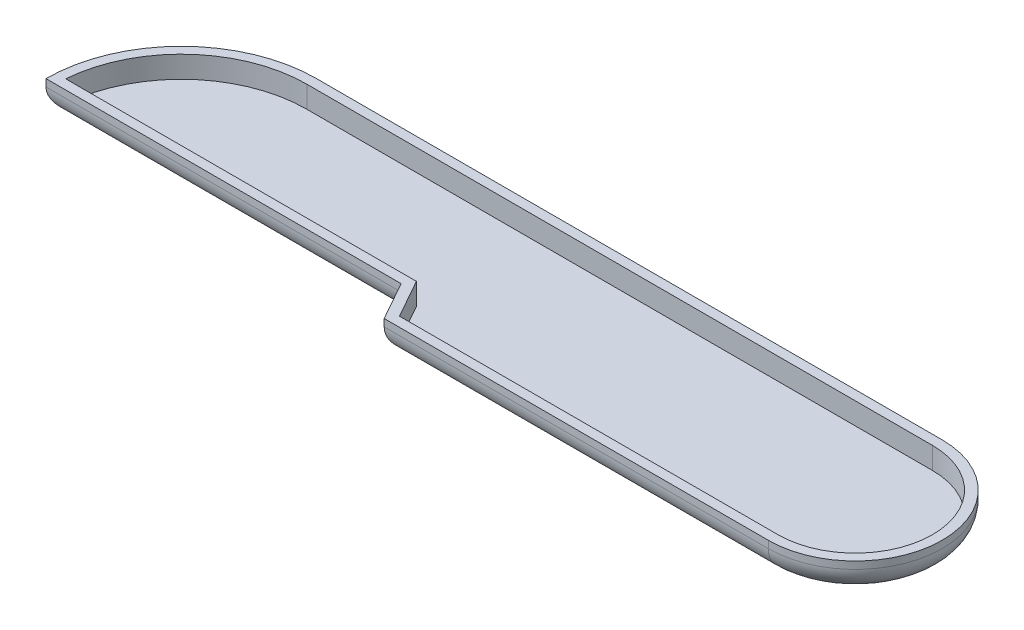
SolidWorks part; units mm, degrees
material "Polyetheretherketone (PEEK)"
ref_plane "Front Plane" through (0, 0, 0) normal (0, 0, 1) x (1, 0, 0)
ref_plane "Top Plane" through (0, 0, 0) normal (0, 1, 0) x (1, 0, 0)
ref_plane "Right Plane" through (0, 0, 0) normal (1, 0, 0) x (0, 0, -1)
sketch "Sketch1" plane through (0, 0, 0) normal (0, 1, 0) x (1, 0, 0)
  line L0 (0, 0) -> (65.786, 0)
  line L5 (65.786, -18.288) -> (25.4, -18.288)
  line L6 (25.4, -18.288) -> (23.114, -14.224)
  line L7 (23.114, -14.224) -> (-14.224, -14.224)
  line L8 (-14.224, -14.224) -> (-14.224, 7.8535) construction
  arc A0 (65.786, 0) -> (65.786, -18.288) centre (65.786, -9.144) cw
  arc A2 (0, 0) -> (-14.224, -14.224) centre (0, -14.224) ccw
  dimension "D4" = 49.53
  dimension "D3" = 89.154
  dimension "D1" = 14.224
  dimension "D2" = 18.288
  dimension "D5" = 37.338
extrude "Boss-Extrude1" add sketch "Sketch1" along normal blind 3.302
fillet "Fillet1" [suppressed] radius 2.54
shell "Shell2" [suppressed] thickness 1.016
shell "Shell3" thickness 1.016
fillet "Fillet2" radius 2.54 6 edges at (4.445, 0, 14.224) (24.257, 0, 16.256) (45.593, 0, 18.288) (74.93, 0, 9.144) (32.893, 0, 0) (-10.0579, 0, 4.1661)
